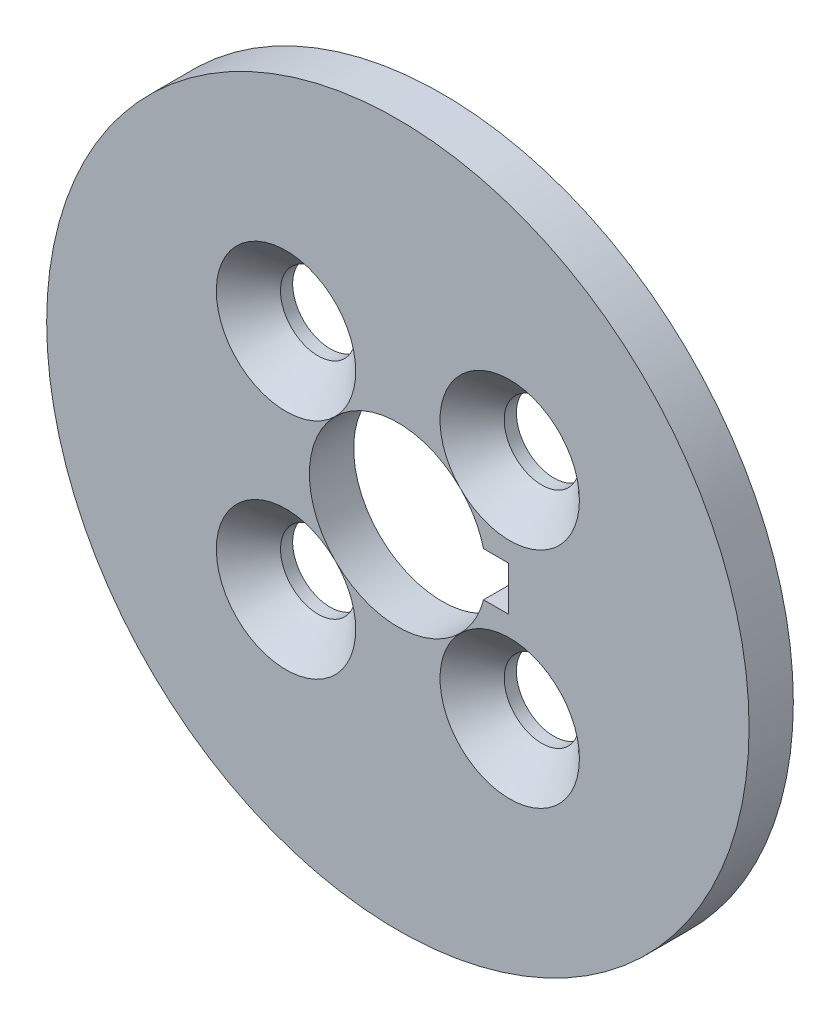
SolidWorks part; units mm, degrees
ref_plane "Front Plane" through (0, 0, 0) normal (0, 0, 1) x (1, 0, 0)
ref_plane "Top Plane" through (0, 0, 0) normal (0, 1, 0) x (1, 0, 0)
ref_plane "Right Plane" through (0, 0, 0) normal (1, 0, 0) x (0, 0, -1)
sketch "Sketch2" plane through (0, 0, 0) normal (0, 0, 1) x (1, 0, 0)
  circle A0 centre (-160.6068, 98.8856) radius 15.875
  circle A1 centre (-165.6626, 103.9414) radius 1.7
  circle A2 centre (-155.5509, 103.9414) radius 1.7
  circle A3 centre (-155.5509, 93.8298) radius 1.7
  circle A4 centre (-165.6626, 93.8298) radius 1.7
  circle A5 centre (-160.6068, 98.8856) radius 4
  circle A6 centre (-160.6068, 98.8856) radius 7.15 construction
  point P15 (-160.7128, 98.9917)
  point P16 (-160.6068, 98.8856)
  dimension "D1" = 3.4
  dimension "D2" = 4
  dimension "D4" = 31.75
  dimension "D5" = 14.3
extrude "Boss-Extrude1" add sketch "Sketch2" along normal blind 2
hole_wizard "CSK for M3 Flat Head Machine Screw2" positions "3DSketch2" profile "Sketch4" countersink size "M3" standard "ANSI Metric" end condition through all
sketch3d "3DSketch2"
  line L0 (-165.6626, 103.9414, 2) -> (-165.6626, 103.9414, 0) construction
  line L1 (-155.5509, 103.9414, 2) -> (-155.5509, 103.9414, 0) construction
  line L2 (-155.5509, 93.8298, 2) -> (-155.5509, 93.8298, 0) construction
  line L3 (-165.6626, 93.8298, 2) -> (-165.6626, 93.8298, 0) construction
  point P0 (-165.6626, 103.9414, 2)
  point P4 (-155.5509, 103.9414, 2)
  point P8 (-155.5509, 93.8298, 2)
  point P12 (-165.6626, 93.8298, 2)
sketch "Sketch4" plane through (-165.6626, 103.9414, 2) normal (1, 0, 0) x (0, -1, 0)
  line L0 (0, 0) -> (0, 2)
  line L1 (0, 2) -> (1.7, 2)
  line L2 (1.7, 2) -> (1.7, 1.45)
  line L3 (1.7, 1.45) -> (3.15, 0)
  line L5 (3.15, 0) -> (0, 0)
  line L6 (-1.7, 1.45) -> (-3.15, 0) construction
  line L11 (0, -6.35) -> (0, 107.95) construction
  dimension "Thru Hole Dia." = 3.4
  dimension "Thru Hole Depth" = 2
  dimension "Near C'Sink Dia." = 6.3
  dimension "Near C'Sink Angle" = 90
sketch "Sketch5" plane through (0, 0, 0) normal (0, 0, -1) x (-1, 0, 0)
  line L0 (155.6068, 99.8856) -> (156.9212, 99.8856)
  line L1 (155.6068, 99.8856) -> (155.6068, 97.8856)
  line L2 (155.6068, 97.8856) -> (156.9212, 97.8856)
  line L3 (156.9212, 97.8856) -> (156.9212, 99.8856)
extrude "Cut-Extrude1" cut sketch "Sketch5" against normal through all
